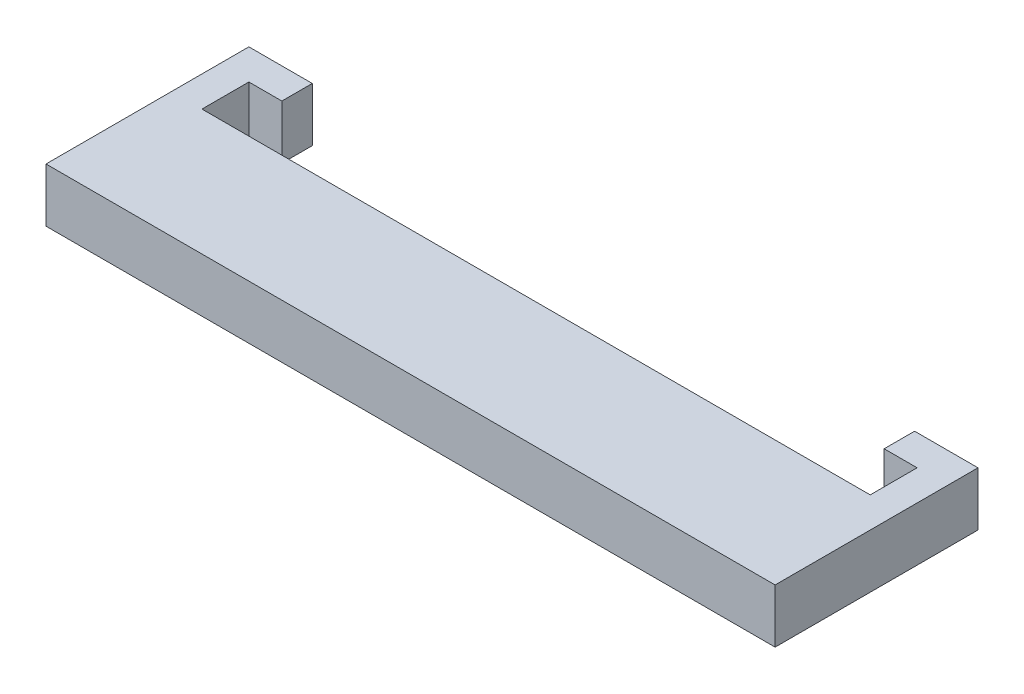
SolidWorks part; units mm, degrees
ref_plane "Front Plane" through (0, 0, 0) normal (0, 0, 1) x (1, 0, 0)
ref_plane "Top Plane" through (0, 0, 0) normal (0, 1, 0) x (1, 0, 0)
ref_plane "Right Plane" through (0, 0, 0) normal (1, 0, 0) x (0, 0, -1)
sketch "Sketch1" plane through (0, 0, 0) normal (0, 1, 0) x (1, 0, 0)
  line L0 (5, 7) -> (5, 12)
  line L1 (0, 0) -> (105, 0)
  line L2 (0, 0) -> (0, 7)
  line L3 (0, 7) -> (105, 7)
  line L4 (105, 0) -> (105, 7)
  line L5 (5, 12) -> (-5, 12)
  line L6 (-5, 12) -> (-5, -20)
  line L7 (-5, -20) -> (110, -20)
  line L8 (52.5, -20) -> (52.5, 7)
  line L9 (110, 12) -> (110, -20)
  line L10 (100, 12) -> (110, 12)
  line L11 (100, 7) -> (100, 12)
  line L12 (-0.2, -0.2) -> (-0.2, 7.2)
  line L13 (-0.2, 7.2) -> (105.2, 7.2)
  line L14 (105.2, -0.2) -> (105.2, 7.2)
  line L15 (-0.2, -0.2) -> (105.2, -0.2)
  dimension "D1" = 105
  dimension "D2" = 7
  dimension "D3" = 5
  dimension "D4" = 20
  dimension "D5" = 5
  dimension "D6" = 10
  dimension "D7" = 0.2
extrude "Boss-Extrude1" add sketch "Sketch1" along normal blind 8.5 contours L15 L12 L13 L0 L5 L6 L7 L8 | L15 L8 L7 L9 L10 L11 L13 L14
